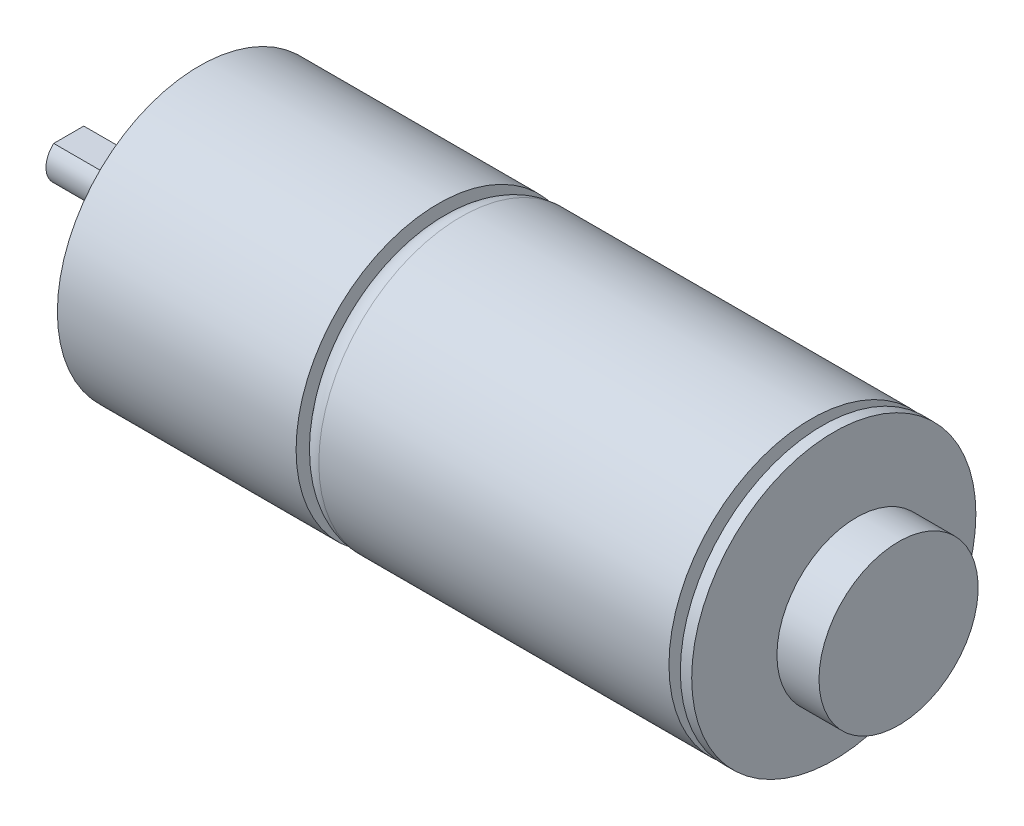
SolidWorks part; units mm, degrees
ref_plane "Front Plane" through (0, 0, 0) normal (0, 0, 1) x (1, 0, 0)
ref_plane "Top Plane" through (0, 0, 0) normal (0, 1, 0) x (1, 0, 0)
ref_plane "Right Plane" through (0, 0, 0) normal (1, 0, 0) x (0, 0, -1)
sketch "Sketch1" plane through (0, 0, 0) normal (0, 0, 1) x (1, 0, 0)
  line L19 (0, 0) -> (0, 2)
  line L20 (0, 2) -> (9, 2)
  line L21 (10.5, 3.5) -> (11.5, 3.5)
  line L22 (11.5, 3.5) -> (11.5, 12.5)
  line L23 (11.5, 12.5) -> (32.5, 12.5)
  line L24 (32.5, 12.5) -> (32.5, 10.5)
  line L25 (34.5, 12.5) -> (65.3, 12.5)
  line L26 (65.3, 12.5) -> (65.3, 3.5)
  line L27 (65.3, 3.5) -> (66.3, 3.5)
  line L28 (66.3, 3.5) -> (66.3, 12.5)
  line L29 (66.3, 12.5) -> (67.3, 12.5)
  line L30 (67.3, 12.5) -> (67.3, 2.5)
  line L31 (67.3, 2.5) -> (69.3, 2.5)
  line L32 (69.3, 2.5) -> (69.3, 7)
  line L33 (69.3, 7) -> (73, 7)
  line L34 (73, 7) -> (73, 0)
  line L35 (0, 0) -> (73, 0)
  arc A2 (9, 2) -> (10.5, 3.5) centre (10.5, 2) cw
  arc A3 (32.5, 10.5) -> (34.5, 12.5) centre (34.5, 10.5) cw
  dimension "D1" = 2
  dimension "D2" = 11.5
  dimension "D3" = 2.5
  dimension "D4" = 3.5
  dimension "D5" = 21
  dimension "D6" = 30.8
  dimension "D7" = 2
  dimension "D8" = 12.5
  dimension "D9" = 73
  dimension "D10" = 1
  dimension "D11" = 2.5
  dimension "D12" = 2
  dimension "D13" = 7
revolve "Revolve1" add sketch "Sketch1" angle 360 about L35
hole_wizard "Tap Drill for M3x0.5 Tap1" positions "Sketch2" profile "Sketch4" hole size "M3x0.5" standard "ANSI Metric"
sketch "Sketch2" plane through (11.5, 0, 0) normal (-1, 0, 0) x (0, 0, 1)
  line L0 (-8.5, 0) -> (8.5, 0) construction
  point P0 (-8.5, 0)
  point P2 (8.5, 0)
  point P9 (0, 0)
  dimension "D1" = 17
sketch "Sketch4" plane through (11.5, 0, -8.5) normal (0, 1, 0) x (0, 0, 1)
  line L0 (0, 0) -> (0, 3.7511)
  line L1 (0, 3.7511) -> (1.25, 3)
  line L2 (1.25, 3) -> (1.25, 0)
  line L5 (1.25, 0) -> (0, 0)
  line L10 (0, 3.7511) -> (-1.25, 3) construction
  line L11 (0, -6.35) -> (0, 107.95) construction
  dimension "Hole Dia." = 2.5
  dimension "Hole Depth" = 3
  dimension "Drill Angle" = 118
sketch "Sketch5" plane through (0, 0, 0) normal (0, 0, 1) x (1, 0, 0)
  line L0 (0, 1.5) -> (8, 1.5)
  line L1 (0, 2) -> (0, -2) construction
  line L2 (8, 1.5) -> (8, 2)
  line L3 (9, 2) -> (0, 2) construction
  line L4 (8, 2) -> (0, 2)
  line L5 (0, 2) -> (0, 1.5)
  dimension "D1" = 8
  dimension "D2" = 0.5
extrude "Cut-Extrude1" cut sketch "Sketch5" against normal through all both and the other way through all
